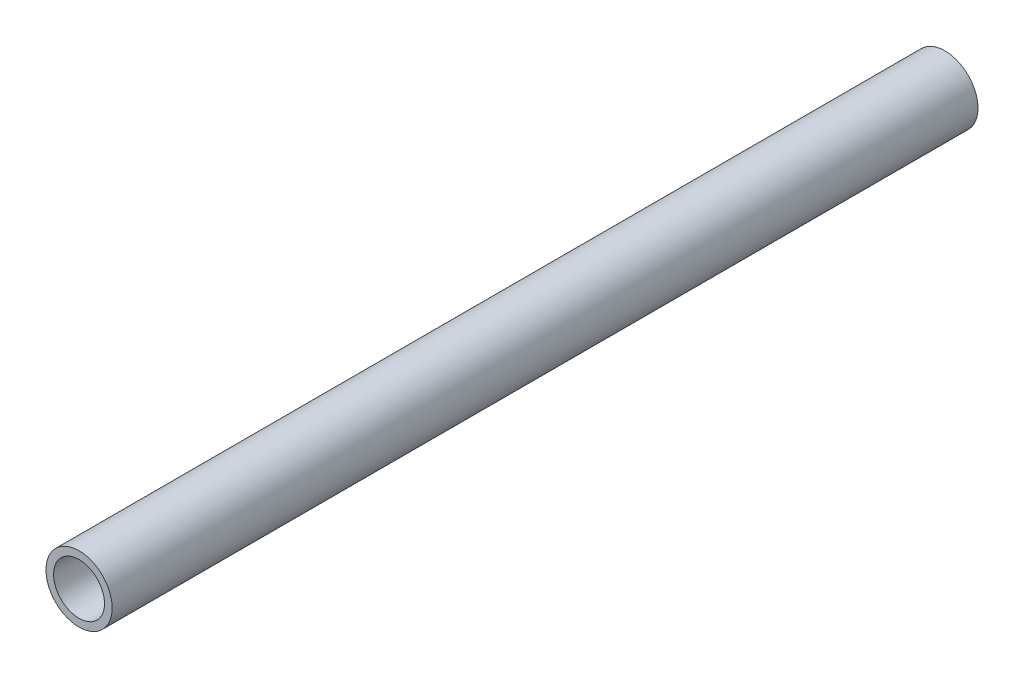
SolidWorks part; units mm, degrees
ref_plane "Front Plane" through (0, 0, 0) normal (0, 0, 1) x (1, 0, 0)
ref_plane "Top Plane" through (0, 0, 0) normal (0, 1, 0) x (1, 0, 0)
ref_plane "Right Plane" through (0, 0, 0) normal (1, 0, 0) x (0, 0, -1)
sketch "Sketch1" plane through (0, 0, 0) normal (0, 0, 1) x (1, 0, 0)
  circle A0 centre (0, 0) radius 6.5
  dimension "D1" = 13
extrude "Extrude-Thin1" add sketch "Sketch1" along normal blind 170 thin thin type one direction reverse wall 1.5
